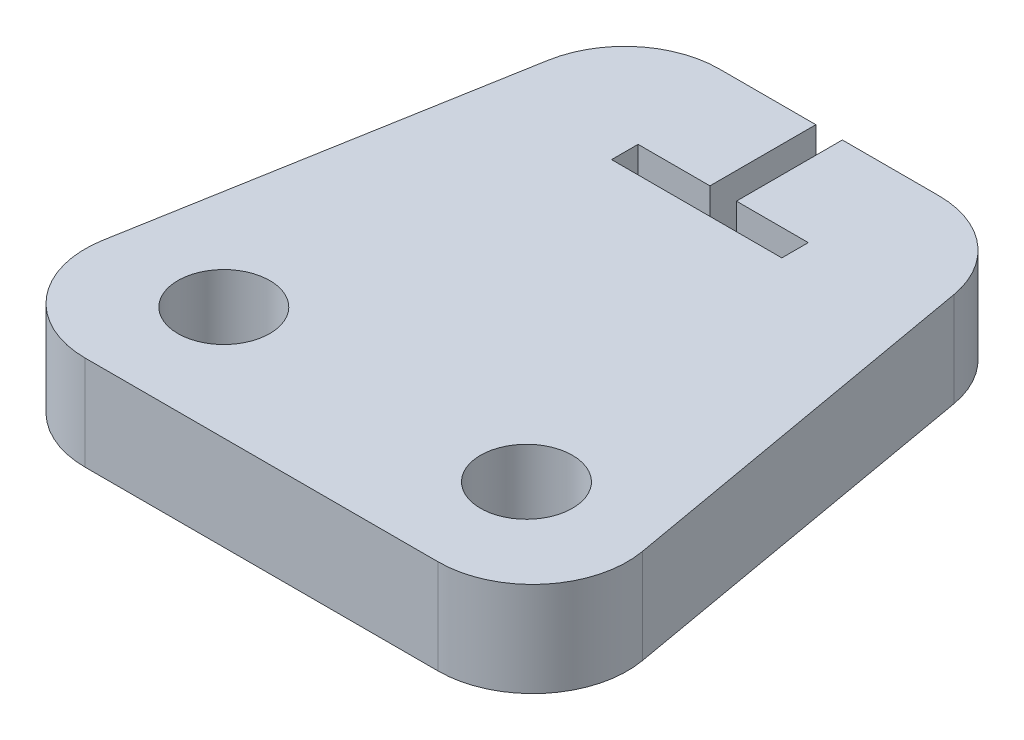
SolidWorks part; units mm, degrees
ref_plane "Front Plane" through (0, 0, 0) normal (0, 0, 1) x (1, 0, 0)
ref_plane "Top Plane" through (0, 0, 0) normal (0, 1, 0) x (1, 0, 0)
ref_plane "Right Plane" through (0, 0, 0) normal (1, 0, 0) x (0, 0, -1)
sketch "Sketch1" plane through (0, 0, 0) normal (0, 1, 0) x (1, 0, 0)
  line L0 (-11.8504, 0) -> (11.8504, 0)
  line L1 (18.104, 7.4527) -> (13.6252, 32.8527)
  line L2 (7.3717, 38.1) -> (-7.3717, 38.1)
  line L3 (-13.6252, 32.8527) -> (-18.104, 7.4527)
  line L4 (0, 0) -> (0, 76.2) construction
  arc A0 (-11.8504, 0) -> (-18.104, 7.4527) centre (-11.8504, 6.35) cw
  arc A1 (11.8504, 0) -> (18.104, 7.4527) centre (11.8504, 6.35) ccw
  arc A2 (13.6252, 32.8527) -> (7.3717, 38.1) centre (7.3717, 31.75) ccw
  arc A3 (-7.3717, 38.1) -> (-13.6252, 32.8527) centre (-7.3717, 31.75) ccw
  point P4 (0, 0)
  point P8 (0, 38.1)
  point P17 (12.7, 38.1)
  point P20 (-12.7, 38.1)
  dimension "D4" = 6.35
  dimension "D1" = 38.1
  dimension "D2" = 80
  dimension "D3" = 25.4
extrude "Boss-Extrude1" add sketch "Sketch1" along normal blind 6.35
sketch "Sketch2" plane through (0, 6.35, 0) normal (0, 1, 0) x (1, 0, 0)
  line L0 (0, 39.4903) -> (0, 0) construction
  line L1 (-11.8504, 0) -> (11.8504, 0) construction
  circle A0 centre (-10.16, 7.62) radius 3.0861
  circle A1 centre (10.16, 7.62) radius 3.0861
  dimension "D1" = 6.1722
  dimension "D2" = 10.16
  dimension "D3" = 7.62
extrude "Cut-Extrude1" cut sketch "Sketch2" against normal through all
sketch "Sketch3" plane through (0, 6.35, 0) normal (0, 1, 0) x (1, 0, 0)
  line L0 (0, 38.1) -> (0, 0) construction
  line L1 (7.3717, 38.1) -> (-7.3717, 38.1) construction
  line L2 (-0.889, 38.1) -> (-0.889, 30.988)
  line L3 (-0.889, 30.988) -> (-5.715, 30.988)
  line L4 (-5.715, 30.988) -> (-5.715, 29.21)
  line L5 (-5.715, 29.21) -> (5.715, 29.21)
  line L6 (5.715, 29.21) -> (5.715, 30.988)
  line L7 (5.715, 30.988) -> (0.889, 30.988)
  line L8 (0.889, 30.988) -> (0.889, 38.1)
  line L9 (0.889, 38.1) -> (-0.889, 38.1)
  point P7 (5.715, 30.099)
  point P14 (0, 29.21)
  point P16 (0, 38.1)
  dimension "D1" = 1.778
  dimension "D2" = 1.778
  dimension "D3" = 11.43
  dimension "D4" = 8.89
extrude "Cut-Extrude2" cut sketch "Sketch3" against normal through all
